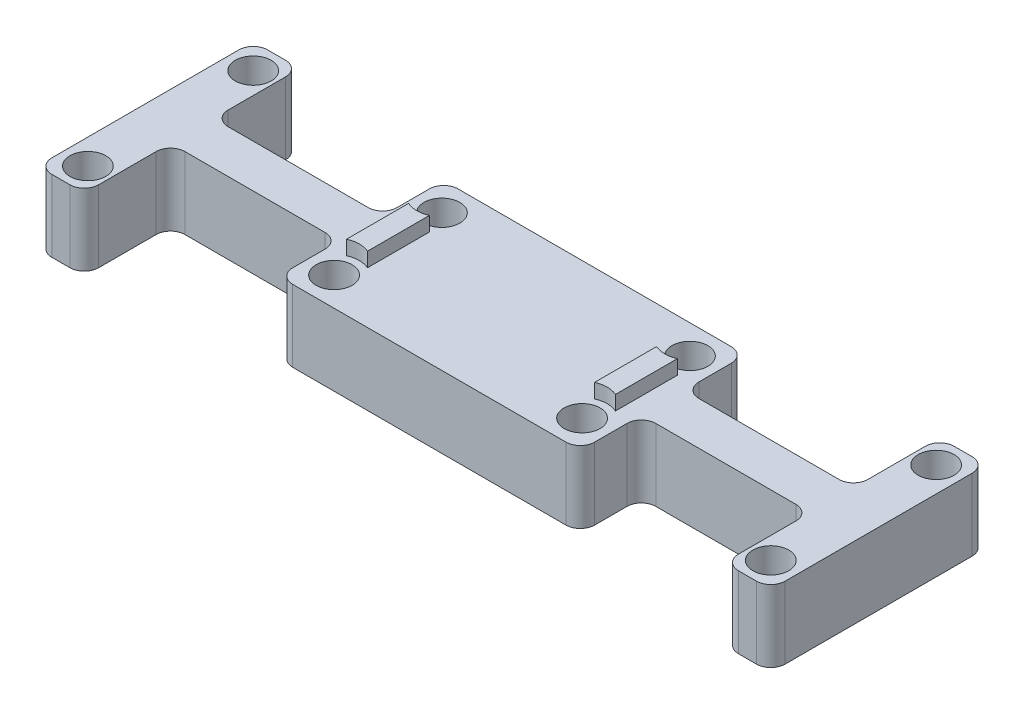
SolidWorks part; units mm, degrees
ref_plane "Front Plane" through (0, 0, 0) normal (0, 0, 1) x (1, 0, 0)
ref_plane "Top Plane" through (0, 0, 0) normal (0, 1, 0) x (1, 0, 0)
ref_plane "Right Plane" through (0, 0, 0) normal (1, 0, 0) x (0, 0, -1)
sketch "Sketch1" plane through (0, 0, 0) normal (0, 1, 0) x (1, 0, 0)
  line L0 (0, 0) -> (-34.5, 0) construction
  line L1 (-34.5, 0) -> (-34.5, 20.5) construction
  line L2 (-36.75, 0) -> (-36.75, 20.5)
  line L3 (-32.25, 0) -> (-32.25, 20.5)
  line L4 (0, 0) -> (0, 20.5) construction
  line L5 (-2.25, 0) -> (-2.25, 20.5)
  line L6 (2.25, 0) -> (2.25, 20.5)
  arc A0 (-36.75, 0) -> (-32.25, 0) centre (-34.5, 0) ccw
  arc A1 (-32.25, 20.5) -> (-36.75, 20.5) centre (-34.5, 20.5) ccw
  arc A2 (-2.25, 0) -> (2.25, 0) centre (0, 0) ccw
  arc A3 (2.25, 20.5) -> (-2.25, 20.5) centre (0, 20.5) ccw
  point P3 (-34.5, 10.25)
  point P9 (0, 10.25)
  point P17 (-34.5, -2.25)
  point P18 (-34.5, 22.75)
  dimension "D1" = 4.5
  dimension "D2" = 4.5
  dimension "D3" = 25
  dimension "D4" = 30
sketch "Sketch2" plane through (0, 0, 0) normal (0, 1, 0) x (1, 0, 0)
  line L0 (-34.5, 0) -> (-34.5, 20.5) construction
  line L1 (0, 0) -> (0, 20.5) construction
  line L2 (-68.25, 7.5) -> (33.75, 7.5) construction
  line L4 (-68.25, 22.5) -> (-68.25, -7.5)
  line L6 (33.75, 22.5) -> (33.75, -7.5)
  line L7 (-34.5, 15) -> (0, 15) construction
  line L8 (-17.25, 15) -> (-17.25, 7.5) construction
  line L9 (-61.75, -7.5) -> (-61.75, 2.5)
  line L10 (-59.75, 4.5) -> (-40.25, 4.5)
  line L11 (-38.25, 2.5) -> (-38.25, -2)
  line L13 (3.75, 2.5) -> (3.75, -2)
  line L14 (25.25, 4.5) -> (5.75, 4.5)
  line L15 (27.25, -7.5) -> (27.25, 2.5)
  line L16 (-61.75, 22.5) -> (-61.75, 12.5)
  line L17 (-59.75, 10.5) -> (-40.25, 10.5)
  line L18 (-38.25, 12.5) -> (-38.25, 17)
  line L19 (27.25, 22.5) -> (27.25, 12.5)
  line L20 (3.75, 12.5) -> (3.75, 17)
  line L21 (25.25, 10.5) -> (5.75, 10.5)
  line L22 (-36.25, 19) -> (1.75, 19)
  line L25 (-36.25, -4) -> (1.75, -4)
  line L27 (30.25, -4) -> (30.25, 7.5) construction
  line L28 (0, 15) -> (0, 0) construction
  line L29 (-34.5, 15) -> (-34.5, 0) construction
  line L30 (-34.5, 0) -> (0, 0) construction
  line L31 (15.5, 4.5) -> (15.5, 7.5) construction
  line L32 (15.5, 7.5) -> (15.5, 10.5) construction
  line L33 (33.75, 22.5) -> (27.25, 22.5)
  line L34 (30.25, 7.5) -> (30.25, 19) construction
  line L35 (33.75, -7.5) -> (27.25, -7.5)
  line L36 (-68.25, 22.5) -> (-61.75, 22.5)
  line L37 (-68.25, -7.5) -> (-61.75, -7.5)
  line L38 (-64.75, 19) -> (30.25, 19) construction
  circle A0 centre (-34.5, 0) radius 2.5
  circle A1 centre (0, 0) radius 2.5
  circle A2 centre (-34.5, 15) radius 2.5
  circle A3 centre (0, 15) radius 2.5
  arc A12 (-40.25, 4.5) -> (-38.25, 2.5) centre (-40.25, 2.5) cw
  arc A13 (-59.75, 4.5) -> (-61.75, 2.5) centre (-59.75, 2.5) ccw
  arc A14 (-36.25, -4) -> (-38.25, -2) centre (-36.25, -2) cw
  arc A16 (1.75, -4) -> (3.75, -2) centre (1.75, -2) ccw
  arc A17 (5.75, 4.5) -> (3.75, 2.5) centre (5.75, 2.5) ccw
  arc A18 (25.25, 4.5) -> (27.25, 2.5) centre (25.25, 2.5) cw
  arc A21 (-59.75, 10.5) -> (-61.75, 12.5) centre (-59.75, 12.5) cw
  arc A22 (-40.25, 10.5) -> (-38.25, 12.5) centre (-40.25, 12.5) ccw
  arc A23 (-36.25, 19) -> (-38.25, 17) centre (-36.25, 17) ccw
  arc A25 (25.25, 10.5) -> (27.25, 12.5) centre (25.25, 12.5) ccw
  arc A26 (1.75, 19) -> (3.75, 17) centre (1.75, 17) cw
  arc A27 (5.75, 10.5) -> (3.75, 12.5) centre (5.75, 12.5) cw
  circle A28 centre (30.25, 19) radius 2.5
  circle A29 centre (30.25, -4) radius 2.5
  circle A30 centre (-64.75, -4) radius 2.5
  circle A31 centre (-64.75, 19) radius 2.5
  point P22 (3.75, 0.25)
  point P29 (-17.25, 7.5)
  dimension "D1" = 5
  dimension "D7" = 23
  dimension "D5" = 95
  dimension "D16" = 2
  dimension "D17" = 2
  dimension "D6" = 3.5
  dimension "D3" = 5
  dimension "D2" = 15
  dimension "D4" = 102
  dimension "D8" = 6.5
  dimension "D9" = 7.5
  dimension "D10" = 42
  dimension "D11" = 23
  dimension "D15" = 3
extrude "Boss-Extrude1" add sketch "Sketch2" against normal blind 10
sketch "Sketch3" plane through (0, 0, 0) normal (0, 1, 0) x (1, 0, 0)
  line L0 (-36.75, 0) -> (-36.75, 20.5) construction
  line L1 (-36.75, 0) -> (-36.75, 20.5)
  line L2 (-32.25, 0) -> (-32.25, 20.5) construction
  line L3 (2.25, 0) -> (2.25, 20.5) construction
  line L4 (-2.25, 0) -> (-2.25, 20.5) construction
  line L5 (-32.25, 0) -> (-32.25, 20.5)
  line L6 (2.25, 0) -> (2.25, 20.5)
  line L7 (-2.25, 0) -> (-2.25, 20.5)
  line L8 (-35.95, 0) -> (-35.95, 20.5)
  line L9 (-1.45, 0) -> (-1.45, 20.5)
  line L10 (-33.05, 0) -> (-33.05, 20.5)
  line L11 (1.45, 0) -> (1.45, 20.5)
  circle A3 centre (-34.5, 15) radius 2.5 construction
  circle A4 centre (0, 15) radius 2.5
  circle A5 centre (0, 0) radius 2.5
  circle A6 centre (-34.5, 0) radius 2.5
  circle A7 centre (-34.5, 15) radius 2.5
  circle A8 centre (-34.5, 15) radius 3.5
  circle A9 centre (-34.5, 0) radius 3.5
  circle A10 centre (0, 0) radius 3.5
  circle A11 centre (0, 15) radius 3.5
  circle A14 centre (0, 15) radius 2.5 construction
  circle A15 centre (0, 0) radius 2.5 construction
  circle A16 centre (-34.5, 0) radius 2.5 construction
  dimension "D1" = 1
  dimension "D2" = 1
  dimension "D3" = 1
  dimension "D4" = 0.8
  dimension "D5" = 0.8
extrude "Boss-Extrude2" add sketch "Sketch3" along normal blind 2 contours A9 L10 A8 L8 | A11 L9 A10 L11
fillet "Fillet1" radius 2 8 edges at (27.25, -5, -22.5) (33.75, -5, -22.5) (27.25, -5, 7.5) (33.75, -5, 7.5) (-61.75, -5, 7.5) (-68.25, -5, 7.5) (-61.75, -5, -22.5) (-68.25, -5, -22.5)
